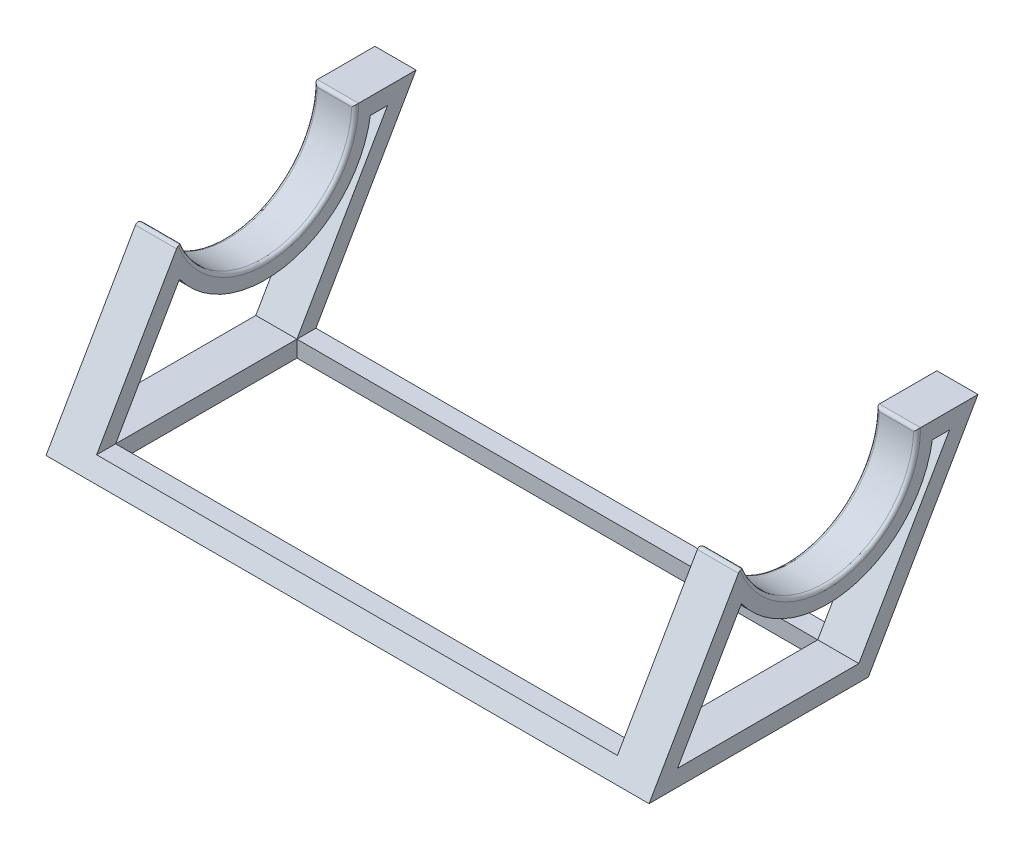
SolidWorks part; units mm, degrees
ref_plane "Front Plane" through (0, 0, 0) normal (0, 0, 1) x (1, 0, 0)
ref_plane "Top Plane" through (0, 0, 0) normal (0, 1, 0) x (1, 0, 0)
ref_plane "Right Plane" through (0, 0, 0) normal (1, 0, 0) x (0, 0, -1)
sketch "Sketch1" plane through (0, 0, 0) normal (1, 0, 0) x (0, 0, -1)
  line L0 (0, 0) -> (101.6, 0)
  line L10 (101.6, 0) -> (152.4, 87.9882)
  line L11 (152.4, 87.9882) -> (124.206, 87.9882)
  line L12 (43.0916, 74.6369) -> (0, 0)
  line L13 (139.2018, 80.3682) -> (131.2333, 80.3682)
  line L14 (97.2006, 7.62) -> (139.2018, 80.3682)
  line L15 (13.1982, 7.62) -> (97.2006, 7.62)
  line L16 (42.7919, 58.8777) -> (13.1982, 7.62)
  arc A1 (43.0916, 74.6369) -> (124.206, 87.9882) centre (82.55, 87.9882) ccw
  arc A2 (42.7919, 58.8777) -> (131.2333, 80.3682) centre (82.55, 87.9882) ccw
  dimension "D3" = 101.6
  dimension "D5" = 83.312
  dimension "D1" = 101.6
  dimension "D2" = 120
  dimension "D4" = 7.62
extrude "Boss-Extrude1" add sketch "Sketch1" along normal blind 279.4
sketch "Sketch2" plane through (0, 87.9882, 0) normal (0, 1, 0) x (1, 0, 0)
  line L0 (0, 152.4) -> (0, 124.206) construction
  line L1 (0, 152.4) -> (0, 124.206)
  line L2 (279.4, 152.4) -> (279.4, 124.206) construction
  line L3 (279.4, 152.4) -> (279.4, 124.206)
  line L4 (0, 152.4) -> (19.05, 152.4)
  line L5 (279.4, 152.4) -> (0, 152.4) construction
  line L6 (279.4, 0) -> (0, 0) construction
  line L7 (19.05, 152.4) -> (260.35, 152.4)
  line L8 (19.05, 152.4) -> (19.05, 0)
  line L9 (19.05, 0) -> (260.35, 0)
  line L10 (260.35, 152.4) -> (260.35, 0)
  line M7 (0, 124.206) -> (279.4, 124.206)
  line M9 (279.4, 152.4) -> (0, 152.4)
  dimension "D1" = 19.05
  dimension "D2" = 241.3
extrude "Cut-Extrude3" cut sketch "Sketch2" along direction (0, 1, 0) on the side against the normal up to vertex (80.3682 mm away) contours L10 L8 L9 M7 | L10 L8 M9 M7
fillet "Fillet1" radius 1.5875 8 edges at (0, 46.8853, -89.3155) (9.525, 87.9882, -124.206) (19.05, 46.8853, -89.3155) (9.525, 74.6369, -43.0916) (269.875, 87.9882, -124.206) (279.4, 46.8853, -89.3155) (269.875, 74.6369, -43.0916) (260.35, 46.8853, -89.3155)
sketch "Sketch4" plane through (0, 7.62, 0) normal (0, 1, 0) x (1, 0, 0)
  line L1 (260.35, 97.2006) -> (19.05, 97.2006)
  line L2 (260.35, 97.2006) -> (260.35, 13.1982)
  line L3 (260.35, 13.1982) -> (19.05, 13.1982)
  line L4 (19.05, 97.2006) -> (19.05, 13.1982)
extrude "Cut-Extrude5" cut sketch "Sketch4" against normal up to surface (7.62 mm away) up to face at (139.7, 0, -50.8)
